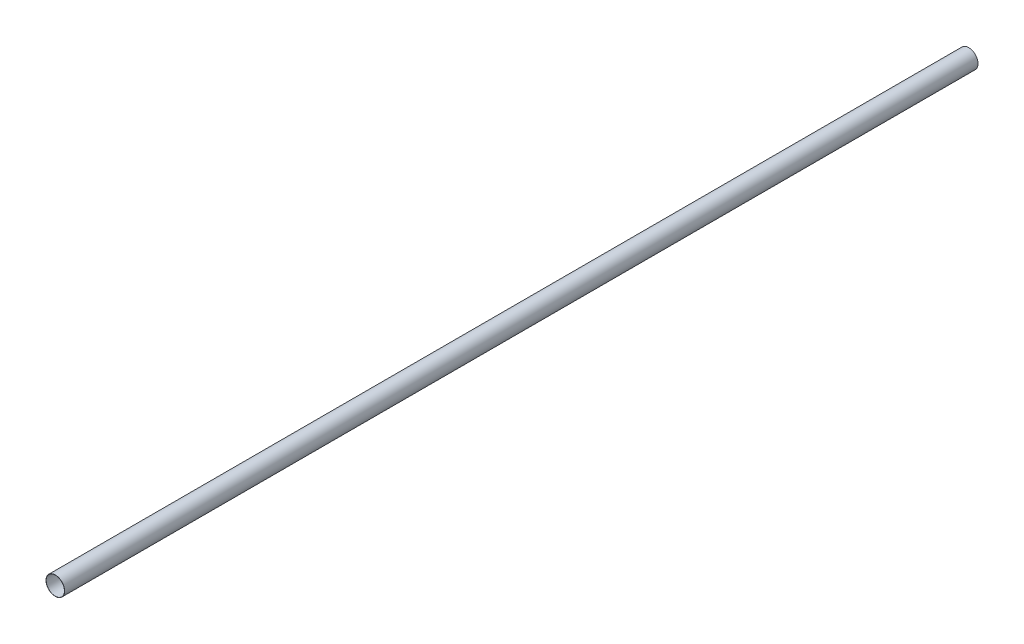
SolidWorks part; units mm, degrees
material "Gray Cast Iron"
ref_plane "Front Plane" through (0, 0, 0) normal (0, 0, 1) x (1, 0, 0)
ref_plane "Top Plane" through (0, 0, 0) normal (0, 1, 0) x (1, 0, 0)
ref_plane "Right Plane" through (0, 0, 0) normal (1, 0, 0) x (0, 0, -1)
sketch "Sketch1" plane through (0, 0, 0) normal (0, 0, 1) x (1, 0, 0)
  circle A0 centre (0, 0) radius 51
  circle A1 centre (0, 0) radius 50
extrude "Boss-Extrude1" add sketch "Sketch1" along normal blind 5000
